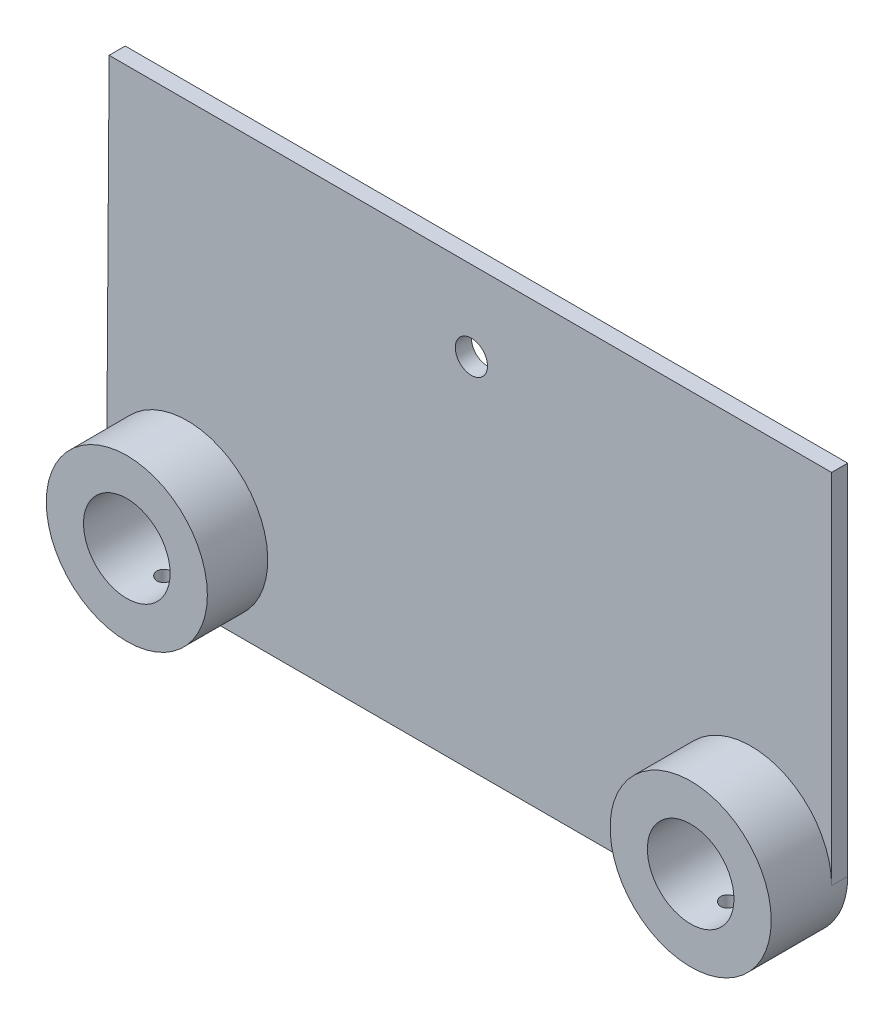
SolidWorks part; units mm, degrees
ref_plane "Front Plane" through (0, 0, 0) normal (0, 0, 1) x (1, 0, 0)
ref_plane "Top Plane" through (0, 0, 0) normal (0, 1, 0) x (1, 0, 0)
ref_plane "Right Plane" through (0, 0, 0) normal (1, 0, 0) x (0, 0, -1)
sketch "Sketch1" plane through (0, 0, 0) normal (0, 0, 1) x (1, 0, 0)
  line L0 (-70, -20) -> (70, -20)
  line L7 (-89.3895, 88.85) -> (-90, 0)
  line L8 (-89.3895, 88.85) -> (90, 88.85)
  line L10 (90, 88.85) -> (90, 0)
  circle A0 centre (70, 0) radius 10.75
  circle A1 centre (-70, 0) radius 10.75
  arc A3 (-90, 0) -> (-70, -20) centre (-70, 0) ccw
  arc A5 (70, -20) -> (90, 0) centre (70, 0) ccw
  dimension "D1" = 21.5
  dimension "D2" = 20
  dimension "D3" = 140
  dimension "D4" = 179.3895
  dimension "D5" = 88.85
extrude "Boss-Extrude1" add sketch "Sketch1" along normal blind 4
sketch "Sketch2" plane through (0, 0, 0) normal (0, 0, 1) x (1, 0, 0)
  line L0 (90, 88.85) -> (-89.3895, 88.85) construction
  circle A0 centre (0.5547, 69) radius 4
  dimension "D1" = 8
  dimension "D2" = 19.85
extrude "Cut-Extrude1" cut sketch "Sketch2" along normal blind 10
sketch "Sketch3" plane through (0, 0, 0) normal (0, 0, 1) x (1, 0, 0)
  circle A0 centre (-70, 0) radius 20
  circle A1 centre (-70, 0) radius 10.75 construction
  arc A2 (-90, 0) -> (-70, -20) centre (-70, 0) ccw construction
  circle A5 centre (-70, 0) radius 10.75
  circle A9 centre (70, 0) radius 20
  circle A10 centre (70, 0) radius 10.75
  circle A11 centre (70, 0) radius 10.75 construction
  dimension "D1" = 40
  dimension "D2" = 21.5
extrude "Boss-Extrude2" add sketch "Sketch3" along normal blind 19
sketch "Sketch4" plane through (0, 0, 0) normal (0, 1, 0) x (1, 0, 0)
  line L0 (-70, -19) -> (-70, 0) construction
  line L1 (-90, -19) -> (-50, -19) construction
  line L2 (70, -19) -> (70, 0) construction
  line L3 (50, -19) -> (90, -19) construction
  circle A0 centre (-70, -9.5) radius 2
  circle A1 centre (70, -9.5) radius 2
  point P15 (70, -9.5)
  point P17 (-70, -9.5)
  dimension "D1" = 4
  dimension "D2" = 140
extrude "Cut-Extrude2" cut sketch "Sketch4" against normal up to surface (20 mm away) up to face at (0, -20, 2)
